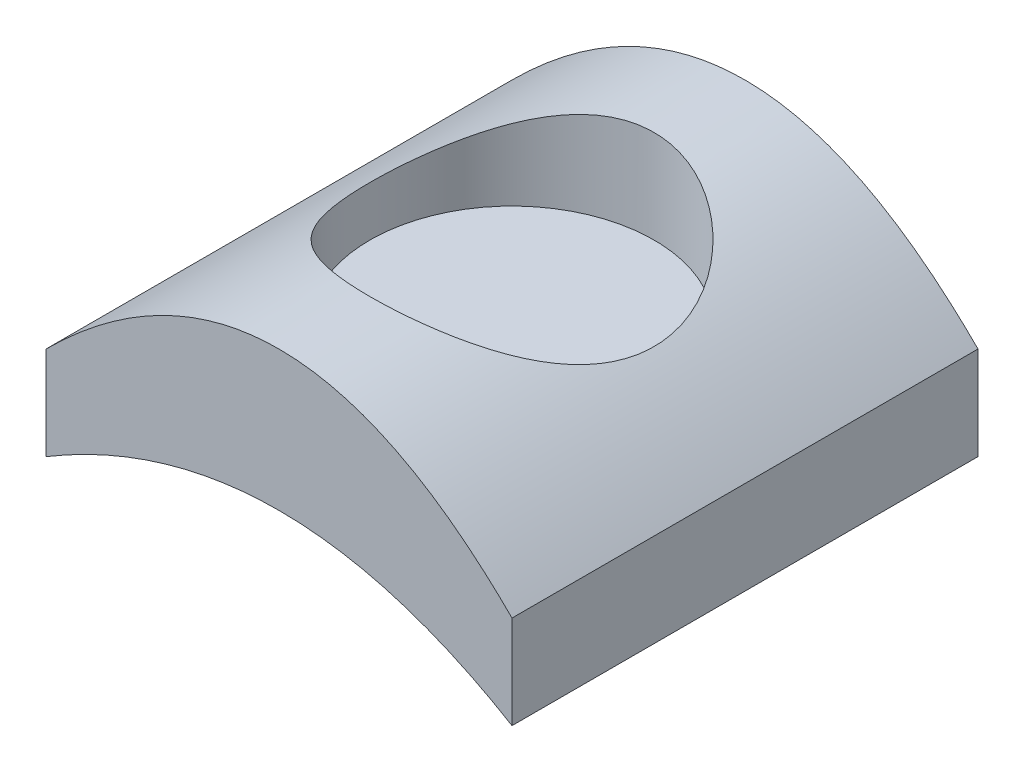
SolidWorks part; units mm, degrees
ref_plane "Front Plane" through (0, 0, 0) normal (0, 0, 1) x (1, 0, 0)
ref_plane "Top Plane" through (0, 0, 0) normal (0, 1, 0) x (1, 0, 0)
ref_plane "Right Plane" through (0, 0, 0) normal (1, 0, 0) x (0, 0, -1)
sketch "Sketch1" plane through (0, 0, 0) normal (0, 0, 1) x (1, 0, 0)
  line L0 (-5, 0) -> (5, 0) construction
  line L1 (0, 0) -> (0, 1.5) construction
  line L2 (-5, 0) -> (-5, 2)
  line L3 (5, 0) -> (5, 2)
  line L4 (0, 1.5) -> (0, 4.5)
  spline S0 degree 2 poles (-5, 0) (0, 3) (5, 0) knots 0 0 0 1 1 1
  spline S1 degree 2 poles (-5, 2) (0, 7) (5, 2) knots 0 0 0 1 1 1
  point P3 (0, 0)
  dimension "D1" = 10
  dimension "D2" = 1.5
  dimension "D3" = 2
  dimension "D4" = 3
extrude "Boss-Extrude1" add sketch "Sketch1" along normal blind 10 contours S1 L3 S0 L2
sketch "Sketch3" plane through (0, 0, 0) normal (0, 1, 0) x (1, 0, 0)
  line L0 (-5, -10) -> (-5, 0) construction
  circle A0 centre (0, -5) radius 3.05
  point P5 (-5, -5)
  dimension "D1" = 6.1
extrude "Cut-Extrude1" cut sketch "Sketch3" against normal blind 2 from offset 4.5 contours A0
